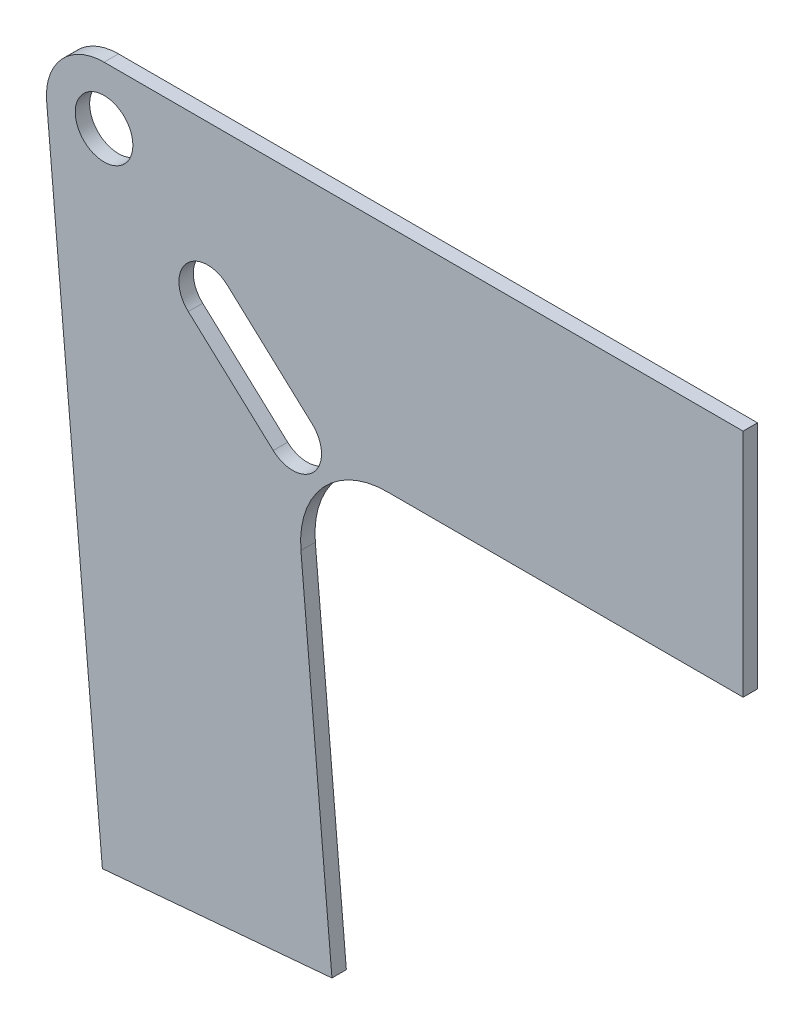
SolidWorks part; units mm, degrees
ref_plane "Front Plane" through (0, 0, 0) normal (0, 0, 1) x (1, 0, 0)
ref_plane "Top Plane" through (0, 0, 0) normal (0, 1, 0) x (1, 0, 0)
ref_plane "Right Plane" through (0, 0, 0) normal (1, 0, 0) x (0, 0, -1)
sketch "Sketch1" plane through (0, 0, 0) normal (0, 0, 1) x (1, 0, 0)
  line L0 (0, 0) -> (-127, 0) construction
  line L1 (-127, 0) -> (-115.9312, -126.5167) construction
  line L2 (-141.2346, -128.7305) -> (-90.6279, -124.303)
  line L3 (0, 25.4) -> (0, -25.4)
  line L4 (-154.7192, 25.4) -> (-99.2808, -25.4) construction
  line L5 (-99.2808, -25.4) -> (-90.6279, -124.303) construction
  line L6 (-99.2808, -25.4) -> (0, -25.4) construction
  line L7 (-154.7192, 25.4) -> (0, 25.4) construction
  line L8 (-154.7192, 25.4) -> (-141.2346, -128.7305) construction
  line L9 (-90.6279, -124.303) -> (-97.4688, -46.1103)
  line L10 (0, -25.4) -> (-78.4913, -25.4)
  line L13 (-141.2346, -128.7305) -> (-153.5113, 11.5931)
  line L14 (-140.8596, 25.4) -> (0, 25.4)
  line L15 (-99.2808, -25.4) -> (-118.0076, -8.24) construction
  line L18 (-103.5708, -30.0817) -> (-122.2976, -12.9217)
  line L19 (-94.9908, -20.7183) -> (-113.7176, -3.5583)
  arc A3 (-153.5113, 11.5931) -> (-140.8596, 25.4) centre (-140.8596, 12.7) cw
  arc A4 (-97.4688, -46.1103) -> (-78.4913, -25.4) centre (-78.4913, -44.45) cw
  circle A7 centre (-140.8596, 12.7) radius 6.35
  arc A8 (-103.5708, -30.0817) -> (-94.9908, -20.7183) centre (-99.2808, -25.4) ccw
  arc A9 (-113.7176, -3.5583) -> (-122.2976, -12.9217) centre (-118.0076, -8.24) ccw
  point P7 (-115.9312, -126.5167)
  point P9 (0, 0)
  point P13 (-127, 0)
  point P14 (-108.6442, -16.82)
  dimension "D8" = 12.7
  dimension "D9" = 19.05
  dimension "D11" = 12.7
  dimension "D2" = 127
  dimension "D3" = 90
  dimension "D4" = 50.8
  dimension "D5" = 50.8
  dimension "D6" = 85
  dimension "D7" = 127
  dimension "D10" = 25.4
  dimension "D12" = 90
extrude "Boss-Extrude1" add sketch "Sketch1" along normal blind 3.175 contours L3 L10 A4 L9 L2 L13 A3 L14
